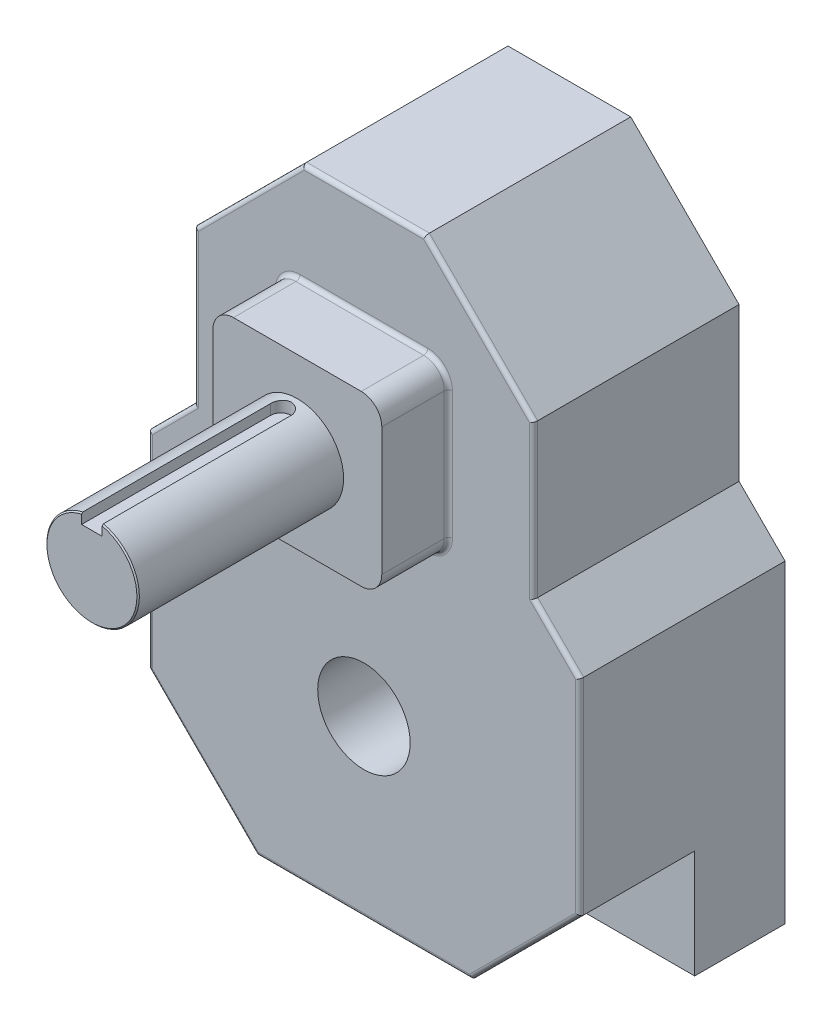
SolidWorks part; units mm, degrees
ref_plane "Front Plane" through (0, 0, 0) normal (0, 0, 1) x (1, 0, 0)
ref_plane "Top Plane" through (0, 0, 0) normal (0, 1, 0) x (1, 0, 0)
ref_plane "Right Plane" through (0, 0, 0) normal (1, 0, 0) x (0, 0, -1)
ref_plane "G" through (0, 107.95, 0) normal (0, 1, 0) x (-1, 0, 0)
ref_plane "E" through (0, 188.976, 0) normal (0, 1, 0) x (-1, 0, 0)
ref_plane "J" through (0, 246.126, 0) normal (0, 1, 0) x (-1, 0, 0)
ref_plane "B" through (0, 0, 63.5) normal (0, 0, 1) x (1, 0, 0)
ref_plane "C" through (0, 0, 147.574) normal (0, 0, 1) x (1, 0, 0)
ref_plane "A" through (0, 0, 84.074) normal (0, 0, 1) x (1, 0, 0)
sketch "L,M" plane through (0, 0, 0) normal (0, 0, 1) x (1, 0, 0)
  line L0 (66.3179, 246.126) -> (-18.9733, 246.126) construction
  line L1 (0, 0) -> (0, 107.95) construction
  line L2 (48.895, 107.95) -> (-48.895, 107.95) construction
  line L3 (-66.675, 53.975) -> (66.675, 53.975)
  line L4 (-18.9733, 246.126) -> (18.9733, 246.126)
  line L5 (48.895, 246.126) -> (-48.895, 246.126) construction
  line L6 (18.9733, 246.126) -> (52.451, 212.6483)
  line L7 (52.451, 212.6483) -> (52.451, 165.3037)
  line L8 (52.451, 165.3037) -> (66.675, 151.0797)
  line L9 (66.675, 151.0797) -> (66.675, 53.975)
  line L11 (66.3179, 246.126) -> (18.9733, 246.126) construction
  line L12 (-66.675, 151.0797) -> (-66.675, 53.975)
  line L13 (-52.451, 165.3037) -> (-66.675, 151.0797)
  line L14 (-52.451, 212.6483) -> (-52.451, 165.3037)
  line L15 (-18.9733, 246.126) -> (-52.451, 212.6483)
  line L16 (48.895, 188.976) -> (-48.895, 188.976) construction
  point P0 (-52.451, 188.976)
  point P7 (0, 53.975)
  point P23 (0, 246.126)
  dimension "D1" = 104.902
  dimension "D2" = 133.35
  dimension "D3" = 45
extrude "Boss-Extrude1" add sketch "L,M" along normal up to surface (63.5 mm away) up to plane "B"
sketch "Sketch3" plane through (0, 0, 63.5) normal (0, 0, 1) x (1, 0, 0)
  line L1 (48.895, 188.976) -> (-48.895, 188.976) construction
  line L2 (-26.0985, 215.0745) -> (26.0985, 215.0745)
  line L3 (-26.0985, 215.0745) -> (-26.0985, 162.8775)
  line L4 (-26.0985, 162.8775) -> (26.0985, 162.8775)
  line L5 (26.0985, 215.0745) -> (26.0985, 162.8775)
  line L6 (0, 188.976) -> (0, 0) construction
  line L7 (-26.0985, 215.0745) -> (26.0985, 162.8775) construction
  point P4 (0, 188.976)
  dimension "D1" = 52.197
extrude "Boss-Extrude2" add sketch "Sketch3" along normal up to surface (20.574 mm away) up to plane "A"
sketch "D" plane through (0, 0, 84.074) normal (0, 0, 1) x (1, 0, 0)
  line L0 (-26.0985, 215.0745) -> (26.0985, 162.8775) construction
  circle A0 centre (0, 188.976) radius 14.2875
  dimension "D1" = 28.575
extrude "Boss-Extrude3" add sketch "D" along normal up to surface (63.5 mm away) up to plane "C"
sketch "Sketch5" plane through (0, 0, 63.5) normal (0, 0, 1) x (1, 0, 0)
  line L0 (66.675, 87.4527) -> (33.1973, 53.975)
  line L1 (66.675, 53.975) -> (66.675, 151.0797) construction
  line L2 (-66.675, 53.975) -> (66.675, 53.975) construction
  line L3 (33.1973, 53.975) -> (66.675, 53.975)
  line L4 (66.675, 53.975) -> (66.675, 87.4527)
  line L5 (-18.9733, 246.126) -> (-52.451, 212.6483) construction
  line L6 (0, 53.975) -> (0, 188.976) construction
  line L7 (-66.675, 53.975) -> (-66.675, 87.4527)
  line L8 (-33.1973, 53.975) -> (-66.675, 53.975)
  line L9 (-66.675, 87.4527) -> (-33.1973, 53.975)
extrude "Cut-Extrude1" cut sketch "Sketch5" against normal blind 35.56
fillet "Fillet1" radius 6.35 4 edges at (-26.0985, 162.8775, 73.787) (26.0985, 162.8775, 73.787) (-26.0985, 215.0745, 73.787) (26.0985, 215.0745, 73.787)
fillet "Fillet2" radius 1.27 20 edges at (24.2386, 164.7374, 63.5) (26.0985, 188.976, 63.5) (24.2386, 213.2146, 63.5) (0, 215.0745, 63.5) (-24.2386, 213.2146, 63.5) (-26.0985, 188.976, 63.5) (-24.2386, 164.7374, 63.5) (0, 162.8775, 63.5) (-66.675, 119.2662, 63.5) (-59.563, 158.1917, 63.5) (-52.451, 188.976, 63.5) (-35.7122, 229.3872, 63.5) (0, 246.126, 63.5) (35.7122, 229.3872, 63.5) (52.451, 188.976, 63.5) (59.563, 158.1917, 63.5) (66.675, 119.2662, 63.5) (49.9362, 70.7138, 63.5) (0, 53.975, 63.5) (-49.9362, 70.7138, 63.5)
sketch "Sketch6" plane through (0, 188.976, 0) normal (0, 1, 0) x (-1, 0, 0)
  line L0 (0, 147.574) -> (0, 89.154) construction
  line L1 (48.895, 147.574) -> (-48.895, 147.574) construction
  line L2 (3.175, 147.574) -> (3.175, 89.154)
  line L3 (-3.175, 147.574) -> (-3.175, 89.154)
  line L4 (0, 0) -> (0, 89.154) construction
  line L6 (-18.9733, 0) -> (18.9733, 0) construction
  line L7 (48.895, 84.074) -> (-48.895, 84.074) construction
  arc A0 (3.175, 147.574) -> (-3.175, 147.574) centre (0, 147.574) ccw
  arc A1 (-3.175, 89.154) -> (3.175, 89.154) centre (0, 89.154) ccw
  point P4 (0, 118.364)
  dimension "D2" = 5.08
  dimension "D1" = 6.35
extrude "Keyway" cut sketch "Sketch6" along normal through all from offset 10.7569
chamfer "Chamfer1" distance 0.381 angle 45 1 edges at (0, 174.6885, 147.574)
sketch "Sketch7" plane through (0, 0, 0) normal (0, 0, -1) x (-1, 0, 0)
  line L0 (48.895, 107.95) -> (-48.895, 107.95) construction
  line L1 (0, 107.95) -> (0, 188.976) construction
  circle A0 centre (0, 107.95) radius 14.2875
  circle A1 centre (0, 188.976) radius 14.2875 construction
extrude "Cut-Extrude3" cut sketch "Sketch7" against normal through all
